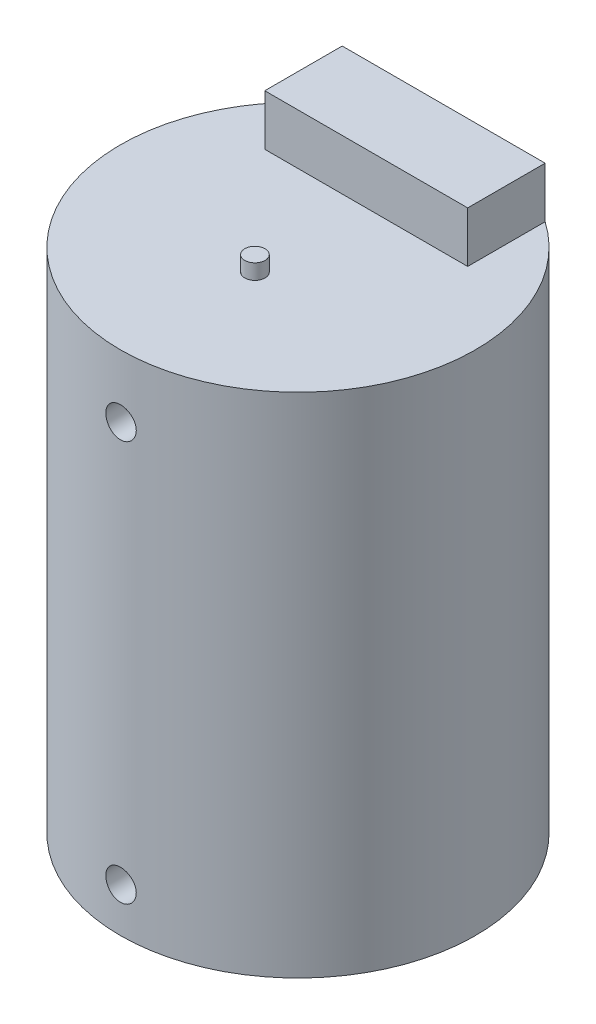
SolidWorks part; units mm, degrees
ref_plane "Front Plane" through (0, 0, 0) normal (0, 0, 1) x (1, 0, 0)
ref_plane "Top Plane" through (0, 0, 0) normal (0, 1, 0) x (1, 0, 0)
ref_plane "Right Plane" through (0, 0, 0) normal (1, 0, 0) x (0, 0, -1)
sketch "Sketch2" plane through (0, 0, 0) normal (0, 1, 0) x (1, 0, 0)
  circle A0 centre (0, 0) radius 350
  dimension "D1" = 700
extrude "Boss-Extrude1" add sketch "Sketch2" along normal blind 1000
sketch "Sketch3" plane through (0, 1000, 0) normal (0, 1, 0) x (1, 0, 0)
  circle A0 centre (0, -84.8411) radius 20
extrude "Boss-Extrude2" add sketch "Sketch3" along normal blind 30 contours A0
sketch "Sketch4" plane through (0, 1000, 0) normal (0, 1, 0) x (1, 0, 0)
  line L1 (0, 134.555) -> (200, 134.555)
  line L2 (0, 134.555) -> (-200, 134.555)
  line L3 (-200, 134.555) -> (-200, 287.2281)
  line L4 (-200, 287.2281) -> (200, 287.2281)
  line L5 (200, 287.2281) -> (200, 134.555)
  circle A0 centre (0, 0) radius 350 construction
extrude "Boss-Extrude3" add sketch "Sketch4" along normal blind 100
sketch "Sketch5" plane through (0, 0, 0) normal (0, 0, 1) x (1, 0, 0)
  circle A0 centre (0, 876.3847) radius 30
extrude "Cut-Extrude1" cut sketch "Sketch5" against normal through all both and the other way through all
sketch "Sketch6" plane through (0, 0, 0) normal (0, 0, 1) x (1, 0, 0)
  line L0 (0, 876.3847) -> (0, 86.8953)
  circle A0 centre (0, 86.8953) radius 30
extrude "Cut-Extrude2" cut sketch "Sketch6" against normal blind 29 and the other way through all contours A0
